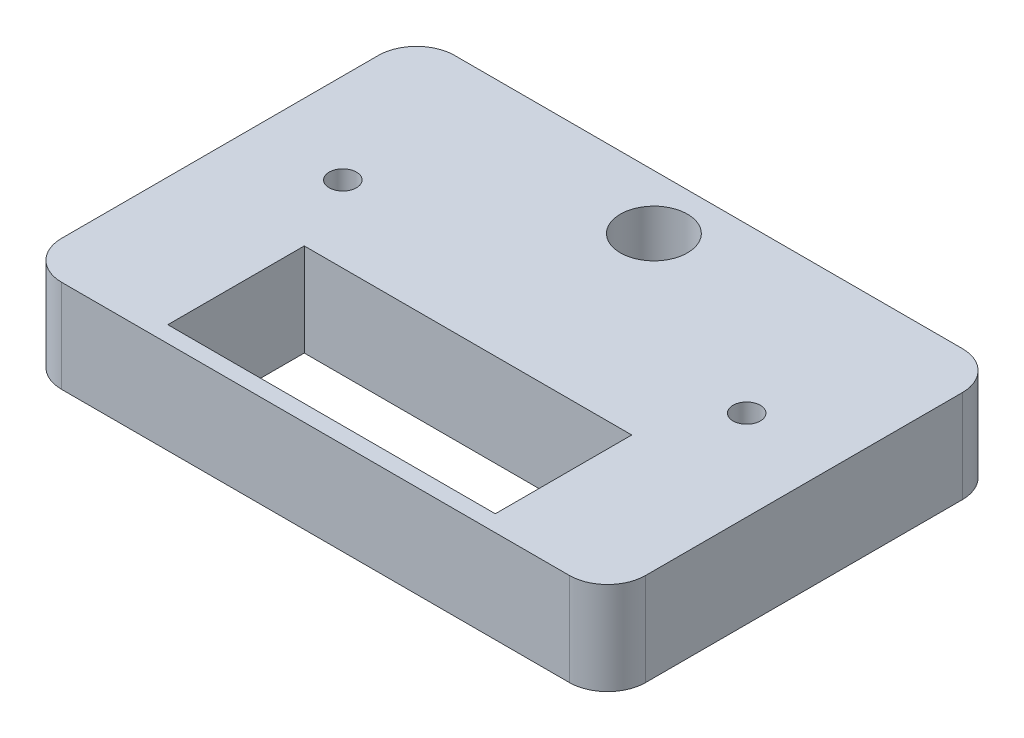
SolidWorks part; units mm, degrees
ref_plane "Front Plane" through (0, 0, 0) normal (0, 0, 1) x (1, 0, 0)
ref_plane "Top Plane" through (0, 0, 0) normal (0, 1, 0) x (1, 0, 0)
ref_plane "Right Plane" through (0, 0, 0) normal (1, 0, 0) x (0, 0, -1)
sketch "Sketch2" plane through (0, 0, 0) normal (0, 1, 0) x (1, 0, 0)
  line L1 (26.75, 18) -> (-26.75, 18)
  line L2 (26.75, 18) -> (26.75, -18)
  line L3 (26.75, -18) -> (-26.75, -18)
  line L4 (-26.75, 18) -> (-26.75, -18)
  line L5 (26.75, 18) -> (-26.75, -18) construction
  line L6 (26.75, -18) -> (-26.75, 18) construction
  point P0 (0, 0)
  dimension "D1" = 53.5
  dimension "D2" = 36
extrude "Boss-Extrude1" add sketch "Sketch2" along normal blind 8.5
sketch "Sketch13" plane through (0, 8.5, 0) normal (0, 1, 0) x (1, 0, 0)
  line L1 (0, -55) -> (0, 55) construction
  line L2 (26.75, 18) -> (-26.75, 18) construction
  circle A0 centre (-18.5, 3) radius 1.25
  circle A1 centre (18.5, 3) radius 1.25
  dimension "D1" = 2.5
  dimension "D2" = 15
sketch "Sketch16" plane through (0, 8.5, 0) normal (0, 1, 0) x (1, 0, 0)
  line L0 (0, -55) -> (0, 55) construction
  line L2 (26.75, 18) -> (-26.75, 18) construction
  circle A0 centre (0, 13) radius 3.075
  dimension "D1" = 6.15
  dimension "D2" = 5
sketch "Sketch25" plane through (0, 0, 0) normal (0, -1, 0) x (1, 0, 0)
  line L0 (-26.75, -7.4867) -> (26.75, -7.4867) construction
  line L1 (-26.75, -18) -> (-26.75, 18) construction
  line L2 (26.75, 18) -> (26.75, -18) construction
  text T0 "4019" font "BankGothic Md BT" height 3.5
extrude "Cut-Extrude15" cut sketch "Sketch25" against normal blind 0.2
extrude "Cut-Extrude16" cut sketch "Sketch16" against normal blind 11.1
extrude "Cut-Extrude18" cut sketch "Sketch13" against normal blind 5
fillet "Fillet1" radius 3.5 4 edges at (26.75, 4.25, 18) (-26.75, 4.25, 18) (-26.75, 4.25, -18) (26.75, 4.25, -18)
sketch "Sketch27" plane through (0, 8.5, 0) normal (0, 1, 0) x (1, 0, 0)
  line L1 (-15.0306, -4) -> (14.9694, -4)
  line L2 (-15.0306, -4) -> (-15.0306, -16.5)
  line L3 (-15.0306, -16.5) -> (14.9694, -16.5)
  line L4 (14.9694, -4) -> (14.9694, -16.5)
  line L5 (-15.0306, -4) -> (14.9694, -16.5) construction
  line L6 (-15.0306, -16.5) -> (14.9694, -4) construction
  circle A0 centre (-18.5, 3) radius 1.25 construction
  point P0 (-0.0306, -10.25)
  dimension "D1" = 30
  dimension "D2" = 7
  dimension "D3" = 12.5
extrude "Cut-Extrude20" cut sketch "Sketch27" against normal blind 21
